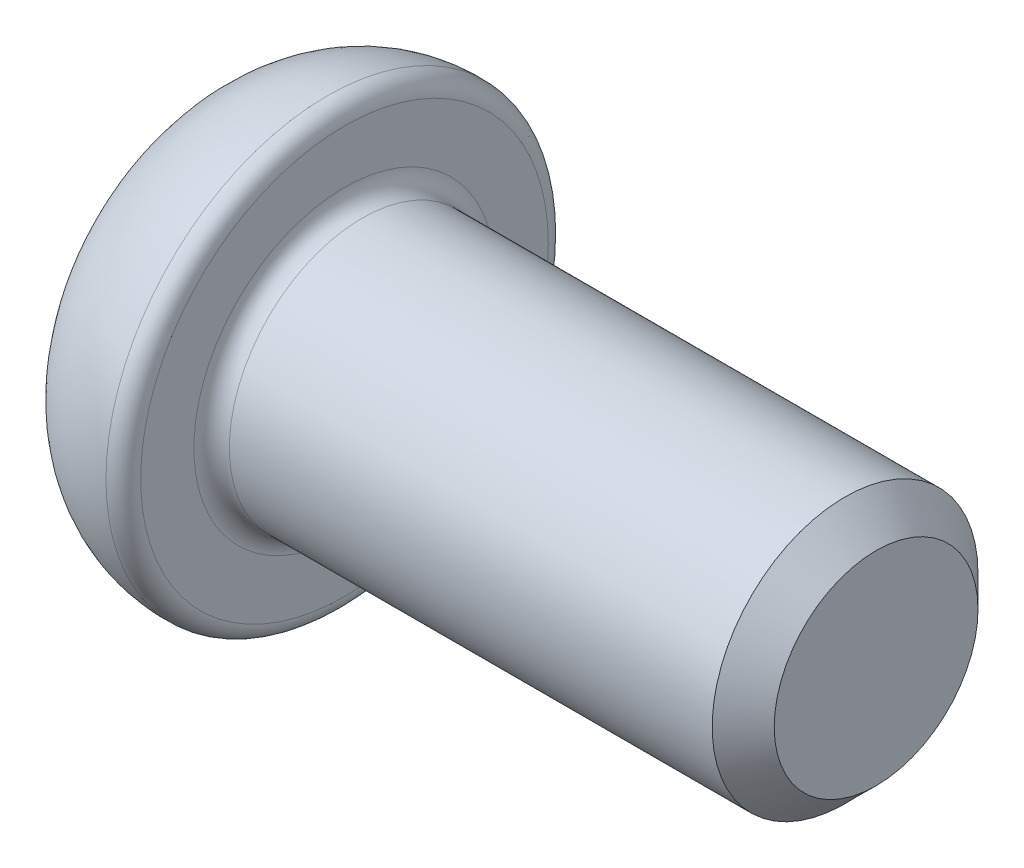
SolidWorks part; units mm, degrees
ref_plane "Front" through (0, 0, 0) normal (0, 0, 1) x (1, 0, 0)
ref_plane "Top" through (0, 0, 0) normal (0, 1, 0) x (1, 0, 0)
ref_plane "Right" through (0, 0, 0) normal (1, 0, 0) x (0, 0, -1)
sketch "Sketch1" plane through (0, 0, 0) normal (0, 0, 1) x (1, 0, 0)
  line L0 (0, 0) -> (0, 1.0011)
  line L1 (1.75, 2.3001) -> (1.75, 1.7)
  line L2 (1.95, 1.5) -> (7.4, 1.5)
  line L3 (7.4, 1.5) -> (7.75, 1.15)
  line L4 (7.75, 1.15) -> (7.75, 0)
  line L5 (7.75, 0) -> (0, 0)
  line L6 (0, 0) -> (-0.6746, 0) construction
  arc A0 (0, 1.0011) -> (1.5577, 2.5) centre (1.5, 1.0011) cw
  arc A1 (1.5577, 2.5) -> (1.75, 2.3001) centre (1.55, 2.3001) cw
  arc A2 (1.75, 1.7) -> (1.95, 1.5) centre (1.95, 1.7) ccw
  dimension "D1" = 3
  dimension "D5" = 0.2
  dimension "D6" = 1.5
  dimension "D2" = 135
  dimension "D3" = 0.35
  dimension "D4" = 1.75
  dimension "D7" = 5
  dimension "D8" = 6
revolve "Revolve1" add sketch "Sketch1" angle 360 about L6
sketch "Sketch2" plane through (0, 0, 0) normal (-1, 0, 0) x (0, 0, 1)
  line L1 (1, -0.5774) -> (1, 0.5774)
  line L2 (1, 0.5774) -> (0, 1.1547)
  line L3 (0, 1.1547) -> (-1, 0.5774)
  line L4 (-1, 0.5774) -> (-1, -0.5774)
  line L5 (-1, -0.5774) -> (0, -1.1547)
  line L6 (0, -1.1547) -> (1, -0.5774)
  circle A0 centre (0, 0) radius 1 construction
  dimension "D1" = 2
extrude "Cut-Extrude1" cut sketch "Sketch2" against normal blind 0.9
